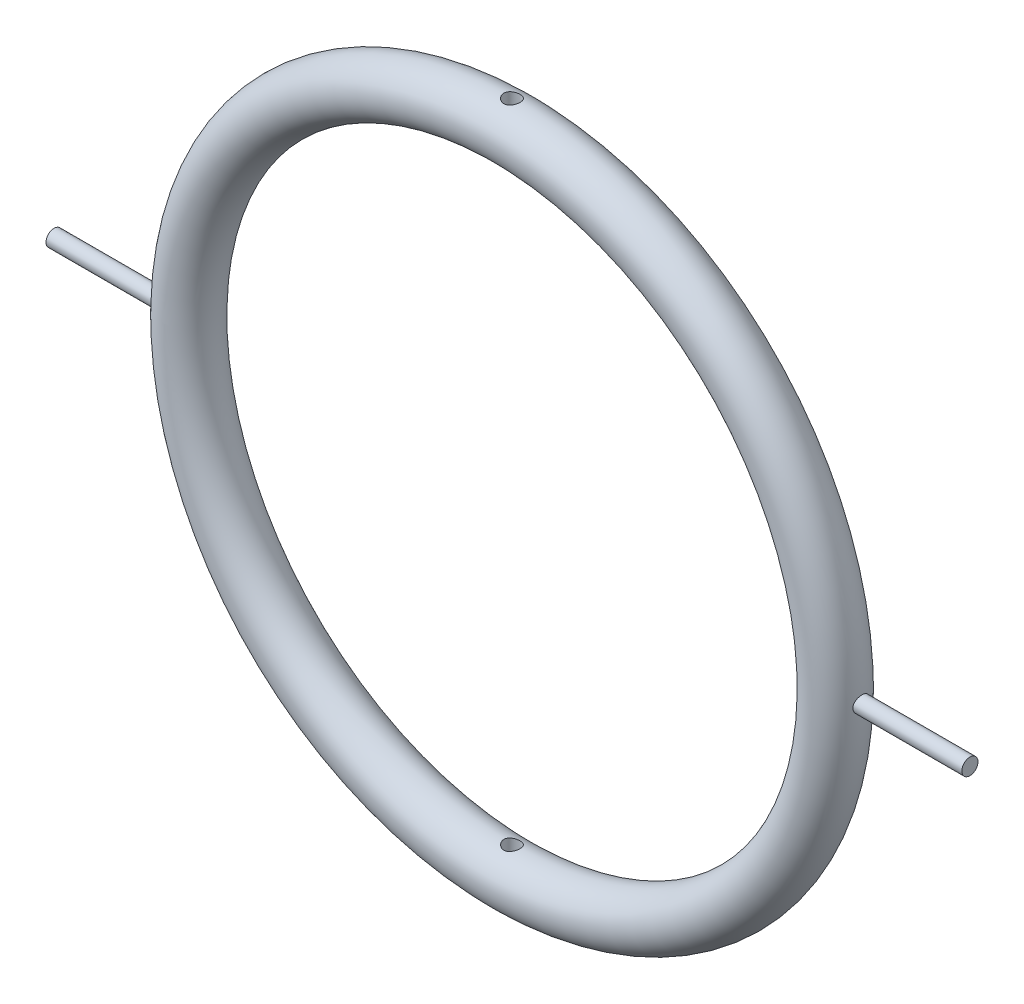
SolidWorks part; units mm, degrees
ref_plane "Front Plane" through (0, 0, 0) normal (0, 0, 1) x (1, 0, 0)
ref_plane "Top Plane" through (0, 0, 0) normal (0, 1, 0) x (1, 0, 0)
ref_plane "Right Plane" through (0, 0, 0) normal (1, 0, 0) x (0, 0, -1)
sketch "Sketch1" plane through (0, 0, 0) normal (0, 1, 0) x (1, 0, 0)
  line L0 (0, 16.2461) -> (0, -19.7924) construction
  circle A0 centre (-30, 0) radius 2.5
  dimension "D1" = 5
  dimension "Diameter" = 30
revolve "Revolve1" add sketch "Sketch1" angle 360 about L0
sketch "Sketch2" plane through (0, 0, 0) normal (0, 0, 1) x (1, 0, 0)
  line L0 (2.75, 0) -> (-2.75, 0) construction
  circle A0 centre (0, 0) radius 32.5 construction
  circle A1 centre (0, 0) radius 32.5 construction
  point P3 (32.5, 0)
  point P4 (42.5, 0)
  dimension "D1" = 10
ref_plane "Plane1" through (42.5, 0, 0) normal (1, 0, 0) x (0, 0, -1)
sketch "Sketch3" plane through (42.5, 0, 0) normal (1, 0, 0) x (0, 0, -1)
  line L0 (0, 32.5) -> (0, -32.5) construction
  circle A0 centre (0, 0) radius 0.75
  dimension "Pin Diameter" = 1.5
extrude "Boss-Extrude1" add sketch "Sketch3" against normal up to next
mirror "Mirror1" about plane through (0, 0, 0) normal (1, 0, 0) of "Boss-Extrude1"
sketch "Sketch4" plane through (0, 0, 0) normal (0, 1, 0) x (1, 0, 0)
  circle A0 centre (0, 0) radius 0.75
  dimension "D1" = 1.5
extrude "Cut-Extrude1" cut sketch "Sketch4" against normal through all and the other way through all
